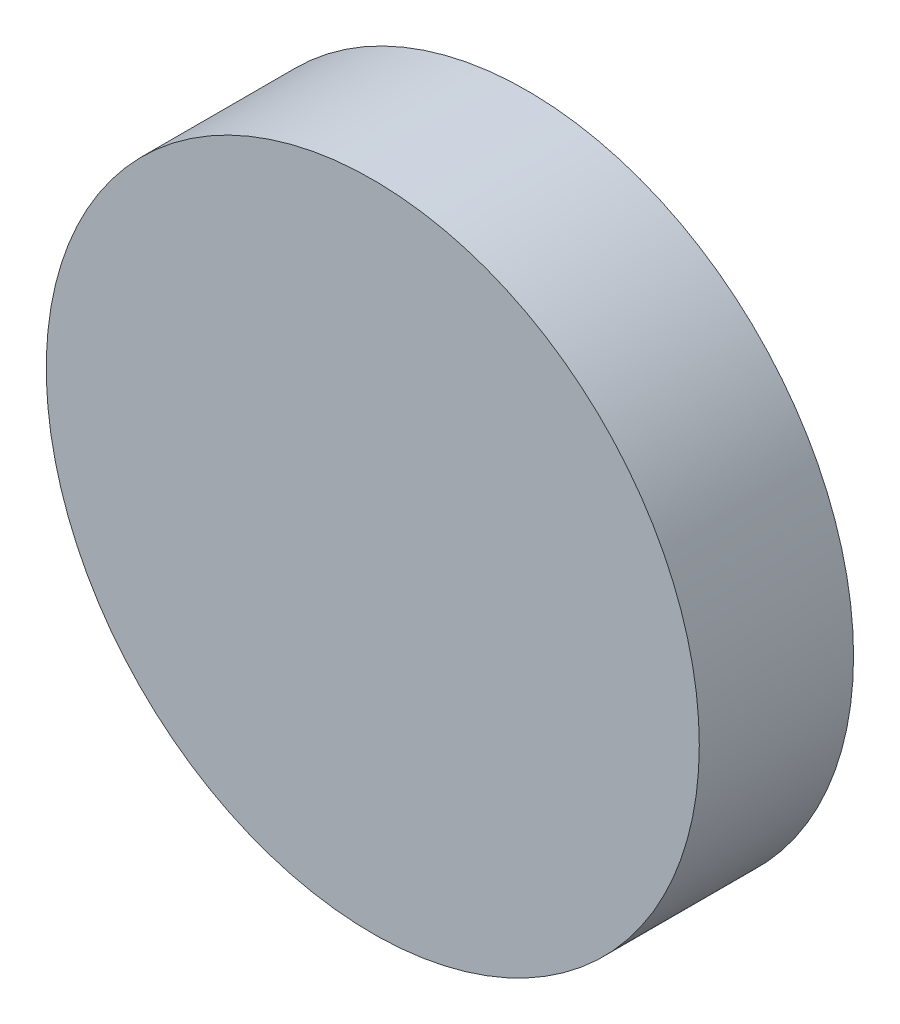
SolidWorks part; units mm, degrees
ref_plane "前视基准面" through (0, 0, 0) normal (0, 0, 1) x (1, 0, 0)
ref_plane "上视基准面" through (0, 0, 0) normal (0, 1, 0) x (1, 0, 0)
ref_plane "右视基准面" through (0, 0, 0) normal (1, 0, 0) x (0, 0, -1)
sketch "草图1" plane through (0, 0, 0) normal (0, 0, 1) x (1, 0, 0)
  circle A0 centre (0, 0) radius 12.7
  dimension "D1" = 25.4
extrude "凸台-拉伸1" add sketch "草图1" along normal blind 6
